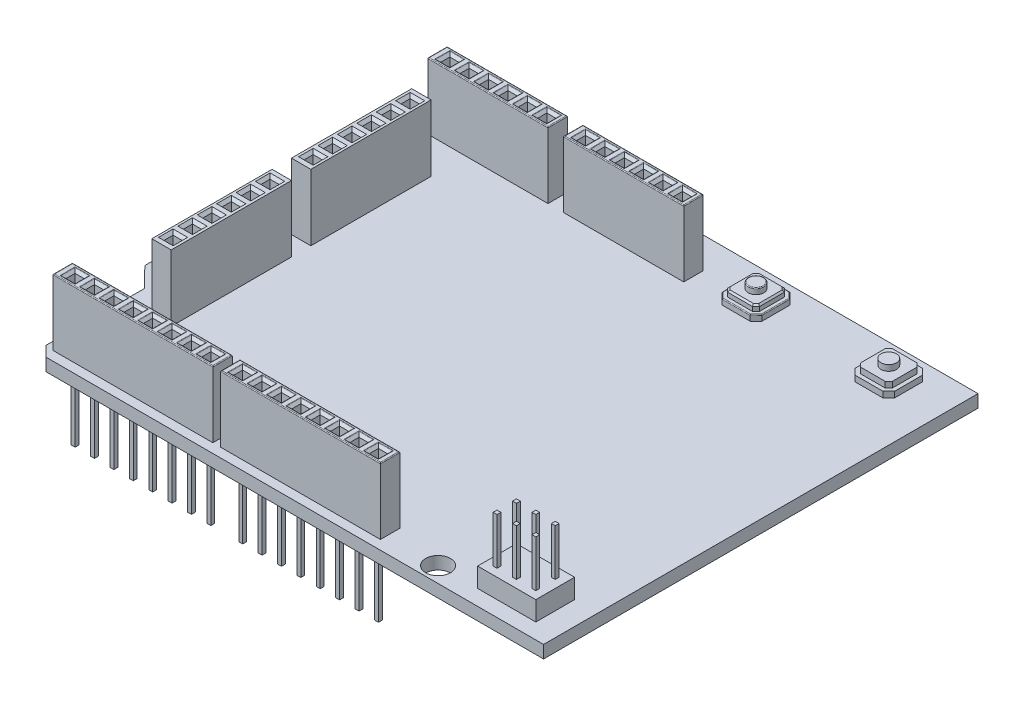
SolidWorks part; units mm, degrees
ref_plane "Front Plane" through (0, 0, 0) normal (0, 0, 1) x (1, 0, 0)
ref_plane "Top Plane" through (0, 0, 0) normal (0, 1, 0) x (1, 0, 0)
ref_plane "Right Plane" through (0, 0, 0) normal (1, 0, 0) x (0, 0, -1)
sketch "Sketch1" plane through (0, 0, 0) normal (0, 1, 0) x (1, 0, 0)
  line L1 (-34, 28) -> (34, 28)
  line L2 (-34, 28) -> (-34, -28)
  line L3 (-34, -28) -> (34, -28)
  line L4 (34, 28) -> (34, -28)
  line L5 (-34, 28) -> (34, -28) construction
  line L6 (-34, -28) -> (34, 28) construction
  point P0 (0, 0)
  dimension "D1" = 68
  dimension "D2" = 56
extrude "Boss-Extrude1" add sketch "Sketch1" along normal blind 1.63
sketch "Sketch2" plane through (0, 1.63, 0) normal (0, 1, 0) x (1, 0, 0)
  line L0 (34, 28) -> (-34, 28) construction
  line L1 (-30.43, 24) -> (-14.93, 24)
  line L2 (-30.43, 24) -> (-30.43, 21.5)
  line L3 (-30.43, 21.5) -> (-14.93, 21.5)
  line L4 (-14.93, 24) -> (-14.93, 21.5)
  line L5 (-30.43, 24) -> (-14.93, 21.5) construction
  line L6 (-30.43, 21.5) -> (-14.93, 24) construction
  line L7 (-34, 28) -> (-34, -28) construction
  line L8 (-12.93, 24) -> (-12.93, 21.5)
  line L9 (-12.93, 24) -> (2.57, 24)
  line L10 (2.57, 24) -> (2.57, 21.5)
  line L11 (-12.93, 21.5) -> (2.57, 21.5)
  line L12 (-30.43, 24) -> (-12.93, 24) construction
  line L13 (11.77, -24.3) -> (11.77, -26.8)
  line L14 (-30.43, -24.3) -> (-9.83, -24.3)
  line L15 (-30.43, -24.3) -> (-30.43, -26.8)
  line L16 (-30.43, -26.8) -> (-9.83, -26.8)
  line L17 (-9.83, -24.3) -> (-9.83, -26.8)
  line L18 (-30.43, -24.3) -> (-9.83, -26.8) construction
  line L19 (-30.43, -26.8) -> (-9.83, -24.3) construction
  line L20 (-8.83, -24.3) -> (11.77, -24.3)
  line L21 (-8.83, -26.8) -> (11.77, -26.8)
  line L22 (-8.83, -24.3) -> (-8.83, -26.8)
  line L23 (-34, -28) -> (34, -28) construction
  line L25 (-28, 17) -> (-25.5, 17)
  line L26 (-28, 17) -> (-28, 1.5)
  line L27 (-28, 1.5) -> (-25.5, 1.5)
  line L28 (-25.5, 17) -> (-25.5, 1.5)
  line L29 (-28, -1) -> (-25.5, -1)
  line L30 (-28, -1) -> (-28, -16.5)
  line L31 (-28, -16.5) -> (-25.5, -16.5)
  line L32 (-25.5, -1) -> (-25.5, -16.5)
  point P0 (-22.68, 22.75)
  point P9 (-20.13, -25.55)
  dimension "D1" = 15.5
  dimension "D2" = 2.5
  dimension "D3" = 4
  dimension "D4" = 3.57
  dimension "D6" = 17.5
  dimension "D7" = 2.5
  dimension "D8" = 20.6
  dimension "D9" = 3.57
  dimension "D10" = 2
  dimension "D11" = 1.2
  dimension "D12" = 1
  dimension "D13" = 11
  dimension "D14" = 2.5
  dimension "D15" = 6
  dimension "D5" = 2
extrude "Boss-Extrude2" add sketch "Sketch2" along normal blind 8.54
sketch "Sketch3" plane through (0, 1.63, 0) normal (0, 1, 0) x (1, 0, 0)
  line L0 (34, 28) -> (-34, 28) construction
  line L1 (7.64, 26.5) -> (11.25, 26.5)
  line L2 (6.89, 25.75) -> (6.89, 22.14)
  line L3 (7.64, 21.39) -> (11.25, 21.39)
  line L4 (12, 25.75) -> (12, 22.14)
  line L5 (6.89, 26.5) -> (12, 21.39) construction
  line L6 (6.89, 21.39) -> (12, 26.5) construction
  line L7 (34, -28) -> (34, 28) construction
  line L8 (11.25, 26.5) -> (12, 25.75)
  line L9 (6.89, 25.75) -> (7.64, 26.5)
  line L10 (6.89, 22.14) -> (7.64, 21.39)
  line L11 (11.25, 21.39) -> (12, 22.14)
  point P0 (9.445, 23.945)
  dimension "D1" = 5.11
  dimension "D2" = 5.11
  dimension "D3" = 1.5
  dimension "D4" = 22
  dimension "D5" = 0.75
  dimension "D6" = 45
  dimension "D7" = 0.75
  dimension "D8" = 45
  dimension "D9" = 0.75
  dimension "D10" = 45
  dimension "D11" = 0.75
  dimension "D12" = 45
extrude "Boss-Extrude3" add sketch "Sketch3" along normal blind 0.75
sketch "Sketch4" plane through (0, 2.38, 0) normal (0, 1, 0) x (1, 0, 0)
  line L47 (7.39, 22.3471) -> (7.9936, 21.7436)
  line L48 (7.39, 25.5429) -> (7.39, 22.3471)
  line L49 (7.8471, 26) -> (7.39, 25.5429)
  line L50 (11.25, 26) -> (7.8471, 26)
  line L51 (7.39, 22.3471) -> (7.8471, 21.89)
  line L52 (7.39, 25.5429) -> (7.39, 22.3471)
  line L53 (7.8471, 26) -> (7.39, 25.5429)
  line L54 (11.0429, 26) -> (7.8471, 26)
  line L65 (11.5, 25.5429) -> (10.8964, 26.1464)
  line L66 (11.5, 22.3471) -> (11.5, 25.5429)
  line L67 (11.0429, 21.89) -> (11.5, 22.3471)
  line L68 (7.64, 21.89) -> (11.0429, 21.89)
  line L69 (11.5, 25.5429) -> (11.0429, 26)
  line L70 (11.5, 22.3471) -> (11.5, 25.5429)
  line L71 (11.0429, 21.89) -> (11.5, 22.3471)
  line L72 (7.8471, 21.89) -> (11.0429, 21.89)
  dimension "D1" = 0.5
  dimension "D2" = 0.5
extrude "Boss-Extrude4" add sketch "Sketch4" along normal blind 0.75
sketch "Sketch5" plane through (0, 3.13, 0) normal (0, 1, 0) x (1, 0, 0)
  line L0 (9.445, 26) -> (9.445, 21.89) construction
  line L1 (11.0429, 26) -> (7.8471, 26) construction
  line L2 (7.8471, 21.89) -> (11.0429, 21.89) construction
  line L3 (7.39, 23.945) -> (11.5, 23.945) construction
  line L4 (7.39, 25.5429) -> (7.39, 22.3471) construction
  line L5 (11.5, 22.3471) -> (11.5, 25.5429) construction
  circle A0 centre (9.445, 23.945) radius 1
  dimension "D1" = 2
extrude "Boss-Extrude5" add sketch "Sketch5" along normal blind 0.75
chamfer "Chamfer1" distance 0.2 angle 45 8 edges at (7.6186, 3.13, -25.7714) (9.445, 3.13, -26) (11.2714, 3.13, -25.7714) (7.39, 3.13, -23.945) (7.6186, 3.13, -22.1186) (9.445, 3.13, -21.89) (11.2714, 3.13, -22.1186) (11.5, 3.13, -23.945)
fillet "Fillet1" radius 0.1 1 edges at (9.445, 3.88, -22.945)
fillet "Fillet2" radius 0.1 8 edges at (7.265, 2.38, -21.765) (6.89, 2.38, -23.945) (7.265, 2.38, -26.125) (9.445, 2.38, -26.5) (11.625, 2.38, -26.125) (9.445, 2.38, -21.39) (11.625, 2.38, -21.765) (12, 2.38, -23.945)
sketch "Sketch7" plane through (0, 10.17, 0) normal (0, 1, 0) x (1, 0, 0)
  line L0 (-30.43, 24) -> (-30.43, 21.5) construction
  line L1 (-29.43, 23.34) -> (-28.25, 23.34)
  line L2 (-29.43, 23.34) -> (-29.43, 22.16)
  line L3 (-29.43, 22.16) -> (-28.25, 22.16)
  line L4 (-28.25, 23.34) -> (-28.25, 22.16)
  line L5 (-29.43, 23.34) -> (-28.25, 22.16) construction
  line L6 (-29.43, 22.16) -> (-28.25, 23.34) construction
  line L7 (-30.43, 22.75) -> (-29.43, 22.75) construction
  line L8 (-26.93, 23.34) -> (-26.93, 22.16)
  line L9 (-26.93, 23.34) -> (-25.75, 23.34)
  line L10 (-25.75, 23.34) -> (-25.75, 22.16)
  line L11 (-26.93, 22.16) -> (-25.75, 22.16)
  line L12 (-24.43, 23.34) -> (-24.43, 22.16)
  line L13 (-24.43, 23.34) -> (-23.25, 23.34)
  line L14 (-23.25, 23.34) -> (-23.25, 22.16)
  line L15 (-24.43, 22.16) -> (-23.25, 22.16)
  line L16 (-21.93, 23.34) -> (-21.93, 22.16)
  line L17 (-21.93, 23.34) -> (-20.75, 23.34)
  line L18 (-20.75, 23.34) -> (-20.75, 22.16)
  line L19 (-21.93, 22.16) -> (-20.75, 22.16)
  line L20 (-19.43, 23.34) -> (-19.43, 22.16)
  line L21 (-19.43, 23.34) -> (-18.25, 23.34)
  line L22 (-18.25, 23.34) -> (-18.25, 22.16)
  line L23 (-19.43, 22.16) -> (-18.25, 22.16)
  line L24 (-16.93, 23.34) -> (-16.93, 22.16)
  line L25 (-16.93, 23.34) -> (-15.75, 23.34)
  line L26 (-15.75, 23.34) -> (-15.75, 22.16)
  line L27 (-16.93, 22.16) -> (-15.75, 22.16)
  line L28 (-30.43, -24.3) -> (-30.43, -26.8) construction
  line L29 (-29.43, -24.96) -> (-28.25, -24.96)
  line L30 (-29.43, -24.96) -> (-29.43, -26.14)
  line L31 (-29.43, -26.14) -> (-28.25, -26.14)
  line L32 (-11.93, 23.34) -> (-11.93, 22.16)
  line L33 (-11.93, 23.34) -> (-10.75, 23.34)
  line L34 (-10.75, 23.34) -> (-10.75, 22.16)
  line L35 (-11.93, 22.16) -> (-10.75, 22.16)
  line L36 (-9.43, 23.34) -> (-9.43, 22.16)
  line L37 (-9.43, 23.34) -> (-8.25, 23.34)
  line L38 (-8.25, 23.34) -> (-8.25, 22.16)
  line L39 (-9.43, 22.16) -> (-8.25, 22.16)
  line L40 (-6.93, 23.34) -> (-6.93, 22.16)
  line L41 (-6.93, 23.34) -> (-5.75, 23.34)
  line L42 (-5.75, 23.34) -> (-5.75, 22.16)
  line L43 (-6.93, 22.16) -> (-5.75, 22.16)
  line L44 (-4.43, 23.34) -> (-4.43, 22.16)
  line L45 (-4.43, 23.34) -> (-3.25, 23.34)
  line L46 (-3.25, 23.34) -> (-3.25, 22.16)
  line L47 (-4.43, 22.16) -> (-3.25, 22.16)
  line L48 (-1.93, 23.34) -> (-1.93, 22.16)
  line L49 (-1.93, 23.34) -> (-0.75, 23.34)
  line L50 (-0.75, 23.34) -> (-0.75, 22.16)
  line L51 (-1.93, 22.16) -> (-0.75, 22.16)
  line L52 (0.57, 23.34) -> (0.57, 22.16)
  line L53 (0.57, 23.34) -> (1.75, 23.34)
  line L54 (1.75, 23.34) -> (1.75, 22.16)
  line L55 (0.57, 22.16) -> (1.75, 22.16)
  line L56 (-14.43, 23.34) -> (-13.25, 23.34) [skipped]
  line L57 (-13.25, 23.34) -> (-13.25, 22.16) [skipped]
  line L58 (-14.43, 22.16) -> (-13.25, 22.16) [skipped]
  line L59 (-14.43, 23.34) -> (-14.43, 22.16) [skipped]
  line L60 (-28.25, -24.96) -> (-28.25, -26.14)
  line L61 (-29.43, -24.96) -> (-28.25, -26.14) construction
  line L62 (-29.43, -26.14) -> (-28.25, -24.96) construction
  line L63 (-30.43, -25.55) -> (-29.43, -25.55) construction
  line L64 (-30.43, -24.3) -> (-30.43, -26.8) construction
  line L65 (-25.75, -24.96) -> (-25.75, -26.14)
  line L66 (-26.93, -24.96) -> (-25.75, -24.96)
  line L67 (-26.93, -26.14) -> (-25.75, -26.14)
  line L68 (-26.93, -24.96) -> (-26.93, -26.14)
  line L69 (-23.25, -24.96) -> (-23.25, -26.14)
  line L70 (-24.43, -24.96) -> (-23.25, -24.96)
  line L71 (-24.43, -26.14) -> (-23.25, -26.14)
  line L72 (-24.43, -24.96) -> (-24.43, -26.14)
  line L73 (-20.75, -24.96) -> (-20.75, -26.14)
  line L74 (-21.93, -24.96) -> (-20.75, -24.96)
  line L75 (-21.93, -26.14) -> (-20.75, -26.14)
  line L76 (-21.93, -24.96) -> (-21.93, -26.14)
  line L77 (-18.25, -24.96) -> (-18.25, -26.14)
  line L78 (-19.43, -24.96) -> (-18.25, -24.96)
  line L79 (-19.43, -26.14) -> (-18.25, -26.14)
  line L80 (-19.43, -24.96) -> (-19.43, -26.14)
  line L81 (-15.75, -24.96) -> (-15.75, -26.14)
  line L82 (-16.93, -24.96) -> (-15.75, -24.96)
  line L83 (-16.93, -26.14) -> (-15.75, -26.14)
  line L84 (-16.93, -24.96) -> (-16.93, -26.14)
  line L85 (-13.25, -24.96) -> (-13.25, -26.14)
  line L86 (-14.43, -24.96) -> (-13.25, -24.96)
  line L87 (-14.43, -26.14) -> (-13.25, -26.14)
  line L88 (-14.43, -24.96) -> (-14.43, -26.14)
  line L89 (-10.75, -24.96) -> (-10.75, -26.14)
  line L90 (-11.93, -24.96) -> (-10.75, -24.96)
  line L91 (-11.93, -26.14) -> (-10.75, -26.14)
  line L92 (-11.93, -24.96) -> (-11.93, -26.14)
  line L93 (-8.83, -24.3) -> (-8.83, -26.8) construction
  line L94 (-7.83, -24.96) -> (-6.65, -24.96)
  line L95 (-7.83, -24.96) -> (-7.83, -26.14)
  line L96 (-7.83, -26.14) -> (-6.65, -26.14)
  line L97 (-6.65, -24.96) -> (-6.65, -26.14)
  line L98 (-7.83, -24.96) -> (-6.65, -26.14) construction
  line L99 (-7.83, -26.14) -> (-6.65, -24.96) construction
  line L100 (-7.83, -25.55) -> (-8.83, -25.55) construction
  line L101 (-8.83, -24.3) -> (-8.83, -26.8) construction
  line L102 (-5.33, -25.55) -> (-6.33, -25.55) construction
  line L103 (-4.15, -24.96) -> (-4.15, -26.14)
  line L104 (-5.33, -24.96) -> (-4.15, -24.96)
  line L105 (-5.33, -26.14) -> (-4.15, -26.14)
  line L106 (-5.33, -24.96) -> (-5.33, -26.14)
  line L107 (-2.83, -25.55) -> (-3.83, -25.55) construction
  line L108 (-1.65, -24.96) -> (-1.65, -26.14)
  line L109 (-2.83, -24.96) -> (-1.65, -24.96)
  line L110 (-2.83, -26.14) -> (-1.65, -26.14)
  line L111 (-2.83, -24.96) -> (-2.83, -26.14)
  line L112 (-0.33, -25.55) -> (-1.33, -25.55) construction
  line L113 (0.85, -24.96) -> (0.85, -26.14)
  line L114 (-0.33, -24.96) -> (0.85, -24.96)
  line L115 (-0.33, -26.14) -> (0.85, -26.14)
  line L116 (-0.33, -24.96) -> (-0.33, -26.14)
  line L117 (2.17, -25.55) -> (1.17, -25.55) construction
  line L118 (3.35, -24.96) -> (3.35, -26.14)
  line L119 (2.17, -24.96) -> (3.35, -24.96)
  line L120 (2.17, -26.14) -> (3.35, -26.14)
  line L121 (2.17, -24.96) -> (2.17, -26.14)
  line L122 (4.67, -25.55) -> (3.67, -25.55) construction
  line L123 (5.85, -24.96) -> (5.85, -26.14)
  line L124 (4.67, -24.96) -> (5.85, -24.96)
  line L125 (4.67, -26.14) -> (5.85, -26.14)
  line L126 (4.67, -24.96) -> (4.67, -26.14)
  line L127 (7.17, -25.55) -> (6.17, -25.55) construction
  line L128 (8.35, -24.96) -> (8.35, -26.14)
  line L129 (7.17, -24.96) -> (8.35, -24.96)
  line L130 (7.17, -26.14) -> (8.35, -26.14)
  line L131 (7.17, -24.96) -> (7.17, -26.14)
  line L132 (9.67, -25.55) -> (8.67, -25.55) construction
  line L133 (10.85, -24.96) -> (10.85, -26.14)
  line L134 (9.67, -24.96) -> (10.85, -24.96)
  line L135 (9.67, -26.14) -> (10.85, -26.14)
  line L136 (9.67, -24.96) -> (9.67, -26.14)
  line L137 (-7.83, -25.55) -> (-5.33, -25.55) construction
  line L138 (-26.1586, 16.1415) -> (-27.3386, 16.1415)
  line L139 (-26.1586, 16.1415) -> (-26.1586, 14.9615)
  line L140 (-26.1586, 14.9615) -> (-27.3386, 14.9615)
  line L141 (-27.3386, 16.1415) -> (-27.3386, 14.9615)
  line L142 (-26.1586, 13.6415) -> (-27.3386, 13.6415)
  line L143 (-26.1586, 13.6415) -> (-26.1586, 12.4615)
  line L144 (-26.1586, 12.4615) -> (-27.3386, 12.4615)
  line L145 (-27.3386, 13.6415) -> (-27.3386, 12.4615)
  line L146 (-26.1586, 11.1415) -> (-27.3386, 11.1415)
  line L147 (-26.1586, 11.1415) -> (-26.1586, 9.9615)
  line L148 (-26.1586, 9.9615) -> (-27.3386, 9.9615)
  line L149 (-27.3386, 11.1415) -> (-27.3386, 9.9615)
  line L150 (-26.1586, 8.6415) -> (-27.3386, 8.6415)
  line L151 (-26.1586, 8.6415) -> (-26.1586, 7.4615)
  line L152 (-26.1586, 7.4615) -> (-27.3386, 7.4615)
  line L153 (-27.3386, 8.6415) -> (-27.3386, 7.4615)
  line L154 (-26.1586, 6.1415) -> (-27.3386, 6.1415)
  line L155 (-26.1586, 6.1415) -> (-26.1586, 4.9615)
  line L156 (-26.1586, 4.9615) -> (-27.3386, 4.9615)
  line L157 (-27.3386, 6.1415) -> (-27.3386, 4.9615)
  line L158 (-26.1586, 3.6415) -> (-27.3386, 3.6415)
  line L159 (-26.1586, 3.6415) -> (-26.1586, 2.4615)
  line L160 (-26.1586, 2.4615) -> (-27.3386, 2.4615)
  line L161 (-27.3386, 3.6415) -> (-27.3386, 2.4615)
  line L162 (-26.1939, -1.8846) -> (-27.3739, -1.8846)
  line L163 (-26.1939, -1.8846) -> (-26.1939, -3.0646)
  line L164 (-26.1939, -3.0646) -> (-27.3739, -3.0646)
  line L165 (-27.3739, -1.8846) -> (-27.3739, -3.0646)
  line L166 (-26.1939, -4.3846) -> (-27.3739, -4.3846)
  line L167 (-26.1939, -4.3846) -> (-26.1939, -5.5646)
  line L168 (-26.1939, -5.5646) -> (-27.3739, -5.5646)
  line L169 (-27.3739, -4.3846) -> (-27.3739, -5.5646)
  line L170 (-26.1939, -6.8846) -> (-27.3739, -6.8846)
  line L171 (-26.1939, -6.8846) -> (-26.1939, -8.0646)
  line L172 (-26.1939, -8.0646) -> (-27.3739, -8.0646)
  line L173 (-27.3739, -6.8846) -> (-27.3739, -8.0646)
  line L174 (-26.1939, -9.3846) -> (-27.3739, -9.3846)
  line L175 (-26.1939, -9.3846) -> (-26.1939, -10.5646)
  line L176 (-26.1939, -10.5646) -> (-27.3739, -10.5646)
  line L177 (-27.3739, -9.3846) -> (-27.3739, -10.5646)
  line L178 (-26.1939, -11.8846) -> (-27.3739, -11.8846)
  line L179 (-26.1939, -11.8846) -> (-26.1939, -13.0646)
  line L180 (-26.1939, -13.0646) -> (-27.3739, -13.0646)
  line L181 (-27.3739, -11.8846) -> (-27.3739, -13.0646)
  line L182 (-26.1939, -14.3846) -> (-27.3739, -14.3846)
  line L183 (-26.1939, -14.3846) -> (-26.1939, -15.5646)
  line L184 (-26.1939, -15.5646) -> (-27.3739, -15.5646)
  line L185 (-27.3739, -14.3846) -> (-27.3739, -15.5646)
  point P0 (-28.84, 22.75)
  point P5 (-30.43, 22.75)
  point P10 (-28.84, -25.55)
  point P73 (-7.24, -25.55)
  dimension "D1" = 1.18
  dimension "D2" = 1.18
  dimension "D3" = 1
  dimension "D5" = 1.18
  dimension "D6" = 1.18
  dimension "D7" = 1
  dimension "D9" = 1.18
  dimension "D10" = 1.18
  dimension "D11" = 1
  dimension "D13" = 2.5
  dimension "D4" = 13
  dimension "D8" = 8
  dimension "D12" = 8
extrude "Cut-Extrude1" cut sketch "Sketch7" against normal blind 6.58
chamfer "Chamfer3" distance 0.35 angle 45 160 edges at (-28.84, 10.17, -22.16) (-28.25, 10.17, -22.75) (-29.43, 10.17, -22.75) (-28.84, 10.17, -23.34) (10.26, 10.17, 26.14) (10.85, 10.17, 25.55) (9.67, 10.17, 25.55) (10.26, 10.17, 24.96) (7.76, 10.17, 26.14) (8.35, 10.17, 25.55) (7.17, 10.17, 25.55) (7.76, 10.17, 24.96) (5.26, 10.17, 26.14) (5.85, 10.17, 25.55) (4.67, 10.17, 25.55) (5.26, 10.17, 24.96) (2.76, 10.17, 26.14) (3.35, 10.17, 25.55) (2.17, 10.17, 25.55) (2.76, 10.17, 24.96) (0.26, 10.17, 26.14) (0.85, 10.17, 25.55) (-0.33, 10.17, 25.55) (0.26, 10.17, 24.96) (-2.24, 10.17, 26.14) (-1.65, 10.17, 25.55) (-2.83, 10.17, 25.55) (-2.24, 10.17, 24.96) (-4.74, 10.17, 26.14) (-4.15, 10.17, 25.55) (-5.33, 10.17, 25.55) (-4.74, 10.17, 24.96) (-7.24, 10.17, 26.14) (-6.65, 10.17, 25.55) (-7.83, 10.17, 25.55) (-7.24, 10.17, 24.96) (-11.34, 10.17, 26.14) (-11.93, 10.17, 25.55) (-10.75, 10.17, 25.55) (-11.34, 10.17, 24.96) (-13.84, 10.17, 26.14) (-14.43, 10.17, 25.55) (-13.25, 10.17, 25.55) (-13.84, 10.17, 24.96) (-16.34, 10.17, 26.14) (-16.93, 10.17, 25.55) (-15.75, 10.17, 25.55) (-16.34, 10.17, 24.96) (-18.84, 10.17, 26.14) (-19.43, 10.17, 25.55) (-18.25, 10.17, 25.55) (-18.84, 10.17, 24.96) (-21.34, 10.17, 26.14) (-21.93, 10.17, 25.55) (-20.75, 10.17, 25.55) (-21.34, 10.17, 24.96) (-23.84, 10.17, 26.14) (-24.43, 10.17, 25.55) (-23.25, 10.17, 25.55) (-23.84, 10.17, 24.96) (-26.34, 10.17, 26.14) (-26.93, 10.17, 25.55) (-25.75, 10.17, 25.55) (-26.34, 10.17, 24.96) (-28.84, 10.17, 26.14) (-29.43, 10.17, 25.55) (-28.25, 10.17, 25.55) (-28.84, 10.17, 24.96) (1.16, 10.17, -23.34) (0.57, 10.17, -22.75) (1.75, 10.17, -22.75) (1.16, 10.17, -22.16) (-1.34, 10.17, -23.34) (-1.93, 10.17, -22.75) (-0.75, 10.17, -22.75) (-1.34, 10.17, -22.16) (-3.84, 10.17, -23.34) (-4.43, 10.17, -22.75) (-3.25, 10.17, -22.75) (-3.84, 10.17, -22.16) (-6.34, 10.17, -23.34) (-6.93, 10.17, -22.75) (-5.75, 10.17, -22.75) (-6.34, 10.17, -22.16) (-8.84, 10.17, -23.34) (-9.43, 10.17, -22.75) (-8.25, 10.17, -22.75) (-8.84, 10.17, -22.16) (-11.34, 10.17, -23.34) (-11.93, 10.17, -22.75) (-10.75, 10.17, -22.75) (-11.34, 10.17, -22.16) (-16.34, 10.17, -22.16) (-16.93, 10.17, -22.75) (-16.34, 10.17, -23.34) (-15.75, 10.17, -22.75) (-19.43, 10.17, -22.75) (-18.84, 10.17, -23.34) (-18.25, 10.17, -22.75) (-18.84, 10.17, -22.16) (-21.93, 10.17, -22.75) (-21.34, 10.17, -23.34) (-20.75, 10.17, -22.75) (-21.34, 10.17, -22.16) (-24.43, 10.17, -22.75) (-23.84, 10.17, -23.34) (-23.25, 10.17, -22.75) (-23.84, 10.17, -22.16) (-26.34, 10.17, -22.16) (-25.75, 10.17, -22.75) (-26.93, 10.17, -22.75) (-26.34, 10.17, -23.34) (-26.7839, 10.17, 15.5646) (-26.1939, 10.17, 14.9746) (-27.3739, 10.17, 14.9746) (-26.7839, 10.17, 14.3846) (-26.7839, 10.17, 13.0646) (-26.1939, 10.17, 12.4746) (-27.3739, 10.17, 12.4746) (-26.7839, 10.17, 11.8846) (-26.7839, 10.17, 10.5646) (-26.1939, 10.17, 9.9746) (-27.3739, 10.17, 9.9746) (-26.7839, 10.17, 9.3846) (-26.7839, 10.17, 8.0646) (-26.1939, 10.17, 7.4746) (-27.3739, 10.17, 7.4746) (-26.7839, 10.17, 6.8846) (-26.7839, 10.17, 5.5646) (-26.1939, 10.17, 4.9746) (-27.3739, 10.17, 4.9746) (-26.7839, 10.17, 4.3846) (-26.7839, 10.17, 3.0646) (-26.1939, 10.17, 2.4746) (-27.3739, 10.17, 2.4746) (-26.7839, 10.17, 1.8846) (-26.7486, 10.17, -2.4615) (-26.1586, 10.17, -3.0515) (-27.3386, 10.17, -3.0515) (-26.7486, 10.17, -3.6415) (-26.7486, 10.17, -6.1415) (-27.3386, 10.17, -5.5515) (-26.7486, 10.17, -4.9615) (-26.1586, 10.17, -5.5515) (-26.7486, 10.17, -7.4615) (-26.1586, 10.17, -8.0515) (-27.3386, 10.17, -8.0515) (-26.7486, 10.17, -8.6415) (-26.7486, 10.17, -9.9615) (-26.1586, 10.17, -10.5515) (-27.3386, 10.17, -10.5515) (-26.7486, 10.17, -11.1415) (-26.7486, 10.17, -12.4615) (-27.3386, 10.17, -13.0515) (-26.7486, 10.17, -13.6415) (-26.1586, 10.17, -13.0515) (-26.1586, 10.17, -15.5515) (-26.7486, 10.17, -16.1415) (-27.3386, 10.17, -15.5515) (-26.7486, 10.17, -14.9615)
sketch "Sketch8" plane through (0, 1.63, 0) normal (0, 1, 0) x (1, 0, 0)
  line L0 (-31.46, 28) -> (-31.46, 24.34)
  line L1 (34, 28) -> (-34, 28) construction
  line L2 (-34, -28) -> (34, -28) construction
  line L3 (-34, 28) -> (-34, -28) construction
  line L4 (-31.46, -14) -> (-31.46, -28)
  line L5 (-31.46, 28) -> (-34, 28)
  line L6 (-31.46, 24.34) -> (-34, 21.3)
  line L7 (-34, -11.4) -> (-31.46, -14)
  line L8 (-34, 28) -> (-34, 21.3)
  line L9 (-31.46, -28) -> (-34, -28)
  line L10 (-34, -28) -> (-34, -11.4)
  dimension "D1" = 2.54
extrude "Cut-Extrude2" cut sketch "Sketch8" against normal through all
chamfer "Chamfer5" distance 1.32 angle 45 1 edges at (-31.46, 0.815, 28)
sketch "Sketch11" plane through (0, 0, 0) normal (0, -1, 0) x (1, 0, 0)
  line L0 (-29.43, 26.14) -> (-28.25, 24.96) construction
  line L1 (-28.25, 26.14) -> (-29.43, 24.96) construction
  line L2 (-26.09, 25.8) -> (-26.09, 25.3)
  line L3 (-29.09, 25.8) -> (-28.59, 25.8)
  line L4 (-29.09, 25.8) -> (-29.09, 25.3)
  line L5 (-29.09, 25.3) -> (-28.59, 25.3)
  line L6 (-28.59, 25.8) -> (-28.59, 25.3)
  line L7 (-29.09, 25.8) -> (-28.59, 25.3) construction
  line L8 (-29.09, 25.3) -> (-28.59, 25.8) construction
  line L9 (-26.59, 25.3) -> (-26.09, 25.3)
  line L10 (-26.59, 25.8) -> (-26.09, 25.8)
  line L11 (-26.59, 25.8) -> (-26.59, 25.3)
  line L12 (-23.59, 25.8) -> (-23.59, 25.3)
  line L13 (-24.09, 25.3) -> (-23.59, 25.3)
  line L14 (-24.09, 25.8) -> (-23.59, 25.8)
  line L15 (-24.09, 25.8) -> (-24.09, 25.3)
  line L16 (-21.09, 25.8) -> (-21.09, 25.3)
  line L17 (-21.59, 25.3) -> (-21.09, 25.3)
  line L18 (-21.59, 25.8) -> (-21.09, 25.8)
  line L19 (-21.59, 25.8) -> (-21.59, 25.3)
  line L20 (-18.59, 25.8) -> (-18.59, 25.3)
  line L21 (-19.09, 25.3) -> (-18.59, 25.3)
  line L22 (-19.09, 25.8) -> (-18.59, 25.8)
  line L23 (-19.09, 25.8) -> (-19.09, 25.3)
  line L24 (-16.09, 25.8) -> (-16.09, 25.3)
  line L25 (-16.59, 25.3) -> (-16.09, 25.3)
  line L26 (-16.59, 25.8) -> (-16.09, 25.8)
  line L27 (-16.59, 25.8) -> (-16.59, 25.3)
  line L28 (-13.59, 25.8) -> (-13.59, 25.3)
  line L29 (-14.09, 25.3) -> (-13.59, 25.3)
  line L30 (-14.09, 25.8) -> (-13.59, 25.8)
  line L31 (-14.09, 25.8) -> (-14.09, 25.3)
  line L32 (-11.09, 25.8) -> (-11.09, 25.3)
  line L33 (-11.59, 25.3) -> (-11.09, 25.3)
  line L34 (-11.59, 25.8) -> (-11.09, 25.8)
  line L35 (-11.59, 25.8) -> (-11.59, 25.3)
  line L36 (-7.83, 26.14) -> (-6.65, 24.96) construction
  line L37 (-6.65, 26.14) -> (-7.83, 24.96) construction
  line L38 (-4.49, 25.8) -> (-4.49, 25.3)
  line L39 (-7.49, 25.8) -> (-6.99, 25.8)
  line L40 (-7.49, 25.8) -> (-7.49, 25.3)
  line L41 (-7.49, 25.3) -> (-6.99, 25.3)
  line L42 (-6.99, 25.8) -> (-6.99, 25.3)
  line L43 (-7.49, 25.8) -> (-6.99, 25.3) construction
  line L44 (-7.49, 25.3) -> (-6.99, 25.8) construction
  line L45 (-4.99, 25.8) -> (-4.49, 25.8)
  line L46 (-4.99, 25.3) -> (-4.49, 25.3)
  line L47 (-4.99, 25.8) -> (-4.99, 25.3)
  line L48 (-1.99, 25.8) -> (-1.99, 25.3)
  line L49 (-2.49, 25.8) -> (-1.99, 25.8)
  line L50 (-2.49, 25.3) -> (-1.99, 25.3)
  line L51 (-2.49, 25.8) -> (-2.49, 25.3)
  line L52 (0.51, 25.8) -> (0.51, 25.3)
  line L53 (0.01, 25.8) -> (0.51, 25.8)
  line L54 (0.01, 25.3) -> (0.51, 25.3)
  line L55 (0.01, 25.8) -> (0.01, 25.3)
  line L56 (3.01, 25.8) -> (3.01, 25.3)
  line L57 (2.51, 25.8) -> (3.01, 25.8)
  line L58 (2.51, 25.3) -> (3.01, 25.3)
  line L59 (2.51, 25.8) -> (2.51, 25.3)
  line L60 (5.51, 25.8) -> (5.51, 25.3)
  line L61 (5.01, 25.8) -> (5.51, 25.8)
  line L62 (5.01, 25.3) -> (5.51, 25.3)
  line L63 (5.01, 25.8) -> (5.01, 25.3)
  line L64 (8.01, 25.8) -> (8.01, 25.3)
  line L65 (7.51, 25.8) -> (8.01, 25.8)
  line L66 (7.51, 25.3) -> (8.01, 25.3)
  line L67 (7.51, 25.8) -> (7.51, 25.3)
  line L68 (10.51, 25.8) -> (10.51, 25.3)
  line L69 (10.01, 25.8) -> (10.51, 25.8)
  line L70 (10.01, 25.3) -> (10.51, 25.3)
  line L71 (10.01, 25.8) -> (10.01, 25.3)
  line L76 (-6.99, 25.8) -> (-4.49, 25.8) construction
  line L77 (-29.43, -22.16) -> (-28.25, -23.34) construction
  line L78 (-28.25, -22.16) -> (-29.43, -23.34) construction
  line L79 (-26.09, -22.5) -> (-26.09, -23)
  line L80 (-29.09, -22.5) -> (-28.59, -22.5)
  line L81 (-29.09, -22.5) -> (-29.09, -23)
  line L82 (-29.09, -23) -> (-28.59, -23)
  line L83 (-28.59, -22.5) -> (-28.59, -23)
  line L84 (-29.09, -22.5) -> (-28.59, -23) construction
  line L85 (-29.09, -23) -> (-28.59, -22.5) construction
  line L86 (-26.59, -22.5) -> (-26.09, -22.5)
  line L87 (-26.59, -23) -> (-26.09, -23)
  line L88 (-26.59, -22.5) -> (-26.59, -23)
  line L89 (-23.59, -22.5) -> (-23.59, -23)
  line L90 (-24.09, -22.5) -> (-23.59, -22.5)
  line L91 (-24.09, -23) -> (-23.59, -23)
  line L92 (-24.09, -22.5) -> (-24.09, -23)
  line L93 (-21.09, -22.5) -> (-21.09, -23)
  line L94 (-21.59, -22.5) -> (-21.09, -22.5)
  line L95 (-21.59, -23) -> (-21.09, -23)
  line L96 (-21.59, -22.5) -> (-21.59, -23)
  line L97 (-18.59, -22.5) -> (-18.59, -23)
  line L98 (-19.09, -22.5) -> (-18.59, -22.5)
  line L99 (-19.09, -23) -> (-18.59, -23)
  line L100 (-19.09, -22.5) -> (-19.09, -23)
  line L101 (-16.09, -22.5) -> (-16.09, -23)
  line L102 (-16.59, -22.5) -> (-16.09, -22.5)
  line L103 (-16.59, -23) -> (-16.09, -23)
  line L104 (-16.59, -22.5) -> (-16.59, -23)
  line L109 (-11.09, -22.5) -> (-11.09, -23)
  line L110 (-11.59, -22.5) -> (-11.09, -22.5)
  line L111 (-11.59, -23) -> (-11.09, -23)
  line L112 (-11.59, -22.5) -> (-11.59, -23)
  line L113 (-8.59, -22.5) -> (-8.59, -23)
  line L114 (-9.09, -22.5) -> (-8.59, -22.5)
  line L115 (-9.09, -23) -> (-8.59, -23)
  line L116 (-9.09, -22.5) -> (-9.09, -23)
  line L117 (-6.09, -22.5) -> (-6.09, -23)
  line L118 (-6.59, -22.5) -> (-6.09, -22.5)
  line L119 (-6.59, -23) -> (-6.09, -23)
  line L120 (-6.59, -22.5) -> (-6.59, -23)
  line L121 (-3.59, -22.5) -> (-3.59, -23)
  line L122 (-4.09, -22.5) -> (-3.59, -22.5)
  line L123 (-4.09, -23) -> (-3.59, -23)
  line L124 (-4.09, -22.5) -> (-4.09, -23)
  line L125 (-1.09, -22.5) -> (-1.09, -23)
  line L126 (-1.59, -22.5) -> (-1.09, -22.5)
  line L127 (-1.59, -23) -> (-1.09, -23)
  line L128 (-1.59, -22.5) -> (-1.59, -23)
  line L129 (1.41, -22.5) -> (1.41, -23)
  line L130 (0.91, -22.5) -> (1.41, -22.5)
  line L131 (0.91, -23) -> (1.41, -23)
  line L132 (0.91, -22.5) -> (0.91, -23)
  line L133 (-28.59, -22.5) -> (-26.09, -22.5) construction
  line L134 (-14.09, -22.5) -> (-13.59, -22.5) [skipped]
  line L135 (-14.09, -22.5) -> (-14.09, -23) [skipped]
  line L136 (-14.09, -23) -> (-13.59, -23) [skipped]
  line L137 (-13.59, -22.5) -> (-13.59, -23) [skipped]
  line L138 (13.01, 25.8) -> (13.01, 25.3) [skipped]
  line L139 (12.51, 25.8) -> (13.01, 25.8) [skipped]
  line L140 (12.51, 25.3) -> (13.01, 25.3) [skipped]
  line L141 (12.51, 25.8) -> (12.51, 25.3) [skipped]
  point P8 (-28.84, 25.55)
  point P49 (-7.24, 25.55)
  point P96 (-28.84, -22.75)
  dimension "D1" = 0.5
  dimension "D2" = 0.5
  dimension "D4" = 0.5
  dimension "D5" = 9
  dimension "D6" = 2.5
  dimension "D7" = 0.5
  dimension "D9" = 2.5
  dimension "D3" = 8
  dimension "D8" = 13
extrude "Boss-Extrude8" add sketch "Sketch11" along normal blind 8.75
fillet "Fillet5" radius 0.1 128 edges at (-12.93, 10.17, -22.75) (-5.18, 10.17, -24) (2.57, 10.17, -22.75) (-5.18, 10.17, -21.5) (-11.34, 10.17, -21.81) (-10.4, 10.17, -22.75) (-11.34, 10.17, -23.69) (-12.28, 10.17, -22.75) (-8.84, 10.17, -21.81) (-7.9, 10.17, -22.75) (-8.84, 10.17, -23.69) (-9.78, 10.17, -22.75) (-6.34, 10.17, -21.81) (-5.4, 10.17, -22.75) (-6.34, 10.17, -23.69) (-7.28, 10.17, -22.75) (-3.84, 10.17, -21.81) (-2.9, 10.17, -22.75) (-3.84, 10.17, -23.69) (-4.78, 10.17, -22.75) (-1.34, 10.17, -21.81) (-0.4, 10.17, -22.75) (-1.34, 10.17, -23.69) (-2.28, 10.17, -22.75) (1.16, 10.17, -21.81) (2.1, 10.17, -22.75) (1.16, 10.17, -23.69) (0.22, 10.17, -22.75) (-22.68, 10.17, -21.5) (-30.43, 10.17, -22.75) (-22.68, 10.17, -24) (-14.93, 10.17, -22.75) (-28.84, 10.17, -23.69) (-29.78, 10.17, -22.75) (-28.84, 10.17, -21.81) (-27.9, 10.17, -22.75) (-26.34, 10.17, -23.69) (-27.28, 10.17, -22.75) (-26.34, 10.17, -21.81) (-25.4, 10.17, -22.75) (-22.9, 10.17, -22.75) (-23.84, 10.17, -23.69) (-24.78, 10.17, -22.75) (-23.84, 10.17, -21.81) (-20.4, 10.17, -22.75) (-21.34, 10.17, -23.69) (-22.28, 10.17, -22.75) (-21.34, 10.17, -21.81) (-17.9, 10.17, -22.75) (-18.84, 10.17, -23.69) (-19.78, 10.17, -22.75) (-18.84, 10.17, -21.81) (-16.34, 10.17, -23.69) (-17.28, 10.17, -22.75) (-16.34, 10.17, -21.81) (-15.4, 10.17, -22.75) (-7.24, 10.17, 24.61) (-8.18, 10.17, 25.55) (-7.24, 10.17, 26.49) (-6.3, 10.17, 25.55) (-4.74, 10.17, 24.61) (-5.68, 10.17, 25.55) (-4.74, 10.17, 26.49) (-3.8, 10.17, 25.55) (-2.24, 10.17, 24.61) (-3.18, 10.17, 25.55) (-2.24, 10.17, 26.49) (-1.3, 10.17, 25.55) (0.26, 10.17, 24.61) (-0.68, 10.17, 25.55) (0.26, 10.17, 26.49) (1.2, 10.17, 25.55) (2.76, 10.17, 24.61) (1.82, 10.17, 25.55) (2.76, 10.17, 26.49) (3.7, 10.17, 25.55) (5.26, 10.17, 24.61) (4.32, 10.17, 25.55) (5.26, 10.17, 26.49) (6.2, 10.17, 25.55) (7.76, 10.17, 24.61) (6.82, 10.17, 25.55) (7.76, 10.17, 26.49) (8.7, 10.17, 25.55) (10.26, 10.17, 24.61) (9.32, 10.17, 25.55) (10.26, 10.17, 26.49) (11.2, 10.17, 25.55) (-20.13, 10.17, 26.8) (-30.43, 10.17, 25.55) (-20.13, 10.17, 24.3) (-9.83, 10.17, 25.55) (-28.84, 10.17, 24.61) (-29.78, 10.17, 25.55) (-28.84, 10.17, 26.49) (-27.9, 10.17, 25.55) (-26.34, 10.17, 24.61) (-27.28, 10.17, 25.55) (-26.34, 10.17, 26.49) (-25.4, 10.17, 25.55) (-23.84, 10.17, 24.61) (-24.78, 10.17, 25.55) (-23.84, 10.17, 26.49) (-22.9, 10.17, 25.55) (-21.34, 10.17, 24.61) (-22.28, 10.17, 25.55) (-21.34, 10.17, 26.49) (-20.4, 10.17, 25.55) (-18.84, 10.17, 24.61) (-19.78, 10.17, 25.55) (-18.84, 10.17, 26.49) (-17.9, 10.17, 25.55) (-16.34, 10.17, 24.61) (-17.28, 10.17, 25.55) (-16.34, 10.17, 26.49) (-15.4, 10.17, 25.55) (-13.84, 10.17, 24.61) (-14.78, 10.17, 25.55) (-13.84, 10.17, 26.49) (-12.9, 10.17, 25.55) (-11.34, 10.17, 24.61) (-12.28, 10.17, 25.55) (-11.34, 10.17, 26.49) (-10.4, 10.17, 25.55) (-8.83, 10.17, 25.55) (1.47, 10.17, 24.3) (11.77, 10.17, 25.55) (1.47, 10.17, 26.8)
ref_plane "Plane1" through (18, 0, 0) normal (1, 0, 0) x (0, 0, -1)
mirror "Mirror1" about plane through (18, 0, 0) normal (1, 0, 0) of "Boss-Extrude4", "Boss-Extrude3", "Boss-Extrude5"
sketch "Sketch12" plane through (0, 1.63, 0) normal (0, 1, 0) x (1, 0, 0)
  line L0 (-34, 21.3) -> (-34, -11.4) construction
  line L1 (-30.14, -28) -> (34, -28) construction
  line L2 (34, -28) -> (34, 28) construction
  line L3 (34, 28) -> (-31.46, 28) construction
  circle A0 centre (-32, -7.5) radius 1.6
  circle A1 centre (18.4, -26) radius 1.6
  dimension "D1" = 3.2
  dimension "D2" = 2
  dimension "D3" = 2
  dimension "D4" = 15.6
  dimension "D5" = 35.5
extrude "Cut-Extrude4" cut sketch "Sketch12" against normal through all
sketch "Sketch18" plane through (0, 1.63, 0) normal (0, 1, 0) x (1, 0, 0)
  line L0 (-30.14, -28) -> (34, -28) construction
  line L1 (31, -26) -> (23.5, -26)
  line L2 (31, -26) -> (31, -21)
  line L3 (31, -21) -> (23.5, -21)
  line L4 (23.5, -26) -> (23.5, -21)
  line L5 (34, -28) -> (34, 28) construction
  dimension "D1" = 2
  dimension "D2" = 3
  dimension "D3" = 7.5
  dimension "D4" = 5
extrude "Boss-Extrude9" add sketch "Sketch18" along normal blind 2.5
sketch "Sketch19" plane through (0, 4.13, 0) normal (0, 1, 0) x (1, 0, 0)
  line L0 (23.5, -21) -> (23.5, -26) construction
  line L1 (24.5, -22) -> (25, -22)
  line L2 (24.5, -22) -> (24.5, -22.5)
  line L3 (24.5, -22.5) -> (25, -22.5)
  line L4 (25, -22) -> (25, -22.5)
  line L5 (31, -21) -> (23.5, -21) construction
  dimension "D1" = 1
  dimension "D2" = 1
  dimension "D3" = 0.5
extrude "Boss-Extrude10" add sketch "Sketch19" along normal blind 6
pattern_linear "LPattern6" count 2 spacing 2.5 along (0, 0, 1) count 3 spacing 2.5 along (1, 0, 0) of "Boss-Extrude10"
